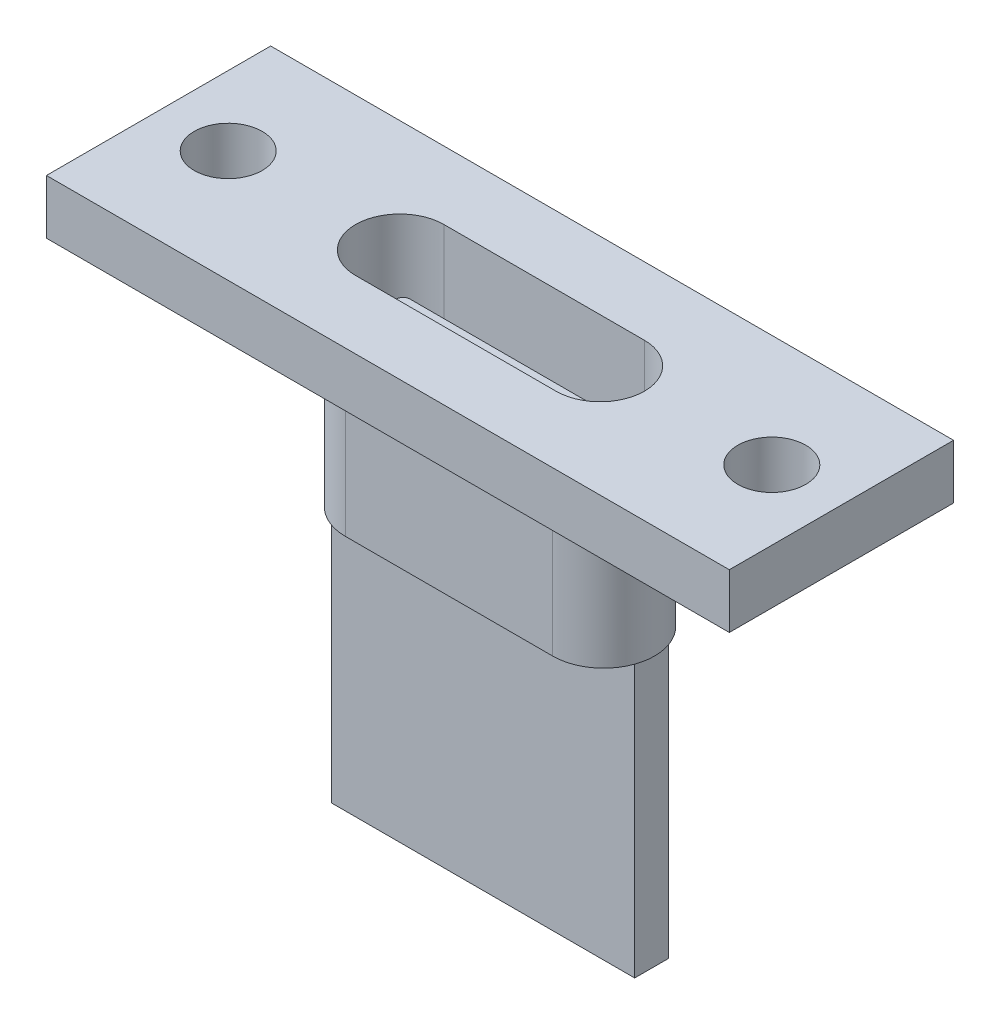
SolidWorks part; units mm, degrees
ref_plane "前视基准面" through (0, 0, 0) normal (0, 0, 1) x (1, 0, 0)
ref_plane "上视基准面" through (0, 0, 0) normal (0, 1, 0) x (1, 0, 0)
ref_plane "右视基准面" through (0, 0, 0) normal (1, 0, 0) x (0, 0, -1)
other "Configuration Table"
sketch "草图1" plane through (0, 0, 0) normal (0, 1, 0) x (1, 0, 0)
  line L1 (-10.05, -3.3) -> (10.05, -3.3)
  line L2 (-10.05, -3.3) -> (-10.05, 3.3)
  line L3 (-10.05, 3.3) -> (10.05, 3.3)
  line L4 (10.05, -3.3) -> (10.05, 3.3)
  line L5 (-10.05, -3.3) -> (10.05, 3.3) construction
  line L6 (-10.05, 3.3) -> (10.05, -3.3) construction
  point P0 (0, 0)
  dimension "D1" = 20.1
  dimension "D2" = 6.6
extrude "凸台-拉伸1" add sketch "草图1" along normal blind 1.6
sketch "草图2" plane through (0, 1.6, 0) normal (0, 1, 0) x (1, 0, 0)
  line L0 (-10.05, 0) -> (10.05, 0) construction
  line L1 (0, 3.3) -> (0, -3.3) construction
  line L2 (10.05, 3.3) -> (-10.05, 3.3) construction
  line L4 (10.05, -3.3) -> (10.05, 3.3)
  line L5 (10.05, 3.3) -> (-10.05, 3.3)
  line L6 (-10.05, 3.3) -> (-10.05, -3.3)
  line L7 (-10.05, -3.3) -> (10.05, -3.3)
  line L8 (10.05, -3.3) -> (10.05, 3.3) construction
  line L9 (10.05, 3.3) -> (-10.05, 3.3) construction
  line L10 (-10.05, 3.3) -> (-10.05, -3.3) construction
  line L11 (-10.05, -3.3) -> (10.05, -3.3) construction
  circle A0 centre (8, 0) radius 1
  circle A1 centre (-8, 0) radius 1
  dimension "D2" = 2
  dimension "D3" = 16
  dimension "D1" = 0
extrude "切除-拉伸1" cut sketch "草图2" against normal up to next
sketch "草图3" plane through (0, 0, 0) normal (0, -1, 0) x (1, 0, 0)
  line L0 (0, 3.3) -> (0, -3.3) construction
  line L1 (-10.05, 0) -> (10.05, 0) construction
  line L2 (-3.05, 0) -> (3.05, 0) construction
  line L3 (-3.05, 1.5) -> (3.05, 1.5)
  line L4 (10.05, -3.3) -> (10.05, 3.3)
  line L5 (10.05, 3.3) -> (-10.05, 3.3)
  line L6 (-10.05, 3.3) -> (-10.05, -3.3)
  line L7 (-10.05, -3.3) -> (10.05, -3.3)
  line L8 (10.05, -3.3) -> (10.05, 3.3) construction
  line L9 (10.05, 3.3) -> (-10.05, 3.3) construction
  line L10 (-10.05, 3.3) -> (-10.05, -3.3) construction
  line L11 (-10.05, -3.3) -> (10.05, -3.3) construction
  line L12 (-3.05, -1.5) -> (3.05, -1.5)
  arc A0 (-3.05, 1.5) -> (-3.05, -1.5) centre (-3.05, 0) ccw
  arc A1 (3.05, -1.5) -> (3.05, 1.5) centre (3.05, 0) ccw
  point P10 (0, 0)
  point P15 (0, 0)
  dimension "D2" = 6.1
  dimension "D3" = 1.5
  dimension "D1" = 0
extrude "凸台-拉伸2" add sketch "草图3" along normal blind 5
sketch "草图4" plane through (0, -5, 0) normal (0, -1, 0) x (1, 0, 0)
  line L1 (-4.4642, -0.5) -> (4.4642, -0.5)
  line L2 (-3.05, -1.5) -> (3.05, -1.5)
  line L3 (3.05, 1.5) -> (-3.05, 1.5)
  line L4 (-3.05, -1.5) -> (3.05, -1.5) construction
  line L5 (3.05, 1.5) -> (-3.05, 1.5) construction
  line L6 (-4.4642, -0.5) -> (-4.4642, 0.5)
  line L7 (-4.4642, 0.5) -> (4.4642, 0.5)
  line L8 (4.4642, -0.5) -> (4.4642, 0.5)
  line L9 (-4.4642, -0.5) -> (4.4642, 0.5) construction
  line L10 (-4.4642, 0.5) -> (4.4642, -0.5) construction
  arc A2 (-3.05, 1.5) -> (-3.05, -1.5) centre (-3.05, 0) ccw
  arc A3 (3.05, -1.5) -> (3.05, 1.5) centre (3.05, 0) ccw
  arc A4 (-3.05, 1.5) -> (-3.05, -1.5) centre (-3.05, 0) ccw construction
  arc A5 (3.05, -1.5) -> (3.05, 1.5) centre (3.05, 0) ccw construction
  point P0 (0, 0)
  dimension "D2" = 1
  dimension "D1" = 0
extrude "凸台-拉伸3" add sketch "草图4" along normal blind 8
sketch "草图5" plane through (0, 1.6, 0) normal (0, 1, 0) x (1, 0, 0)
  line L0 (-10.05, 0) -> (10.05, 0) construction
  line L1 (0, 3.3) -> (0, -3.3) construction
  line L2 (-2.95, 0) -> (2.95, 0) construction
  line L3 (-2.95, 1.3) -> (2.95, 1.3)
  line L4 (10.05, -3.3) -> (10.05, 3.3)
  line L5 (10.05, 3.3) -> (-10.05, 3.3)
  line L6 (-10.05, 3.3) -> (-10.05, -3.3)
  line L7 (-10.05, -3.3) -> (10.05, -3.3)
  line L8 (10.05, -3.3) -> (10.05, 3.3) construction
  line L9 (10.05, 3.3) -> (-10.05, 3.3) construction
  line L10 (-10.05, 3.3) -> (-10.05, -3.3) construction
  line L11 (-10.05, -3.3) -> (10.05, -3.3) construction
  line L12 (-2.95, -1.3) -> (2.95, -1.3)
  arc A1 (-2.95, 1.3) -> (-2.95, -1.3) centre (-2.95, 0) ccw
  arc A2 (2.95, -1.3) -> (2.95, 1.3) centre (2.95, 0) ccw
  point P10 (0, 0)
  point P15 (0, 0)
  point P16 (0, 0)
  dimension "D2" = 1.3
  dimension "D3" = 5.9
  dimension "D1" = 0
extrude "切除-拉伸2" cut sketch "草图5" against normal blind 5
sketch "草图6" plane through (0, -3.4, 0) normal (0, 1, 0) x (1, 0, 0)
  line L1 (-3.05, -0.4) -> (3.05, -0.4)
  line L2 (-2.95, -1.3) -> (2.95, -1.3)
  line L3 (2.95, 1.3) -> (-2.95, 1.3)
  line L4 (-2.95, -1.3) -> (2.95, -1.3) construction
  line L5 (2.95, 1.3) -> (-2.95, 1.3) construction
  line L6 (-3.25, -0.2) -> (-3.25, 0.2)
  line L7 (-3.05, 0.4) -> (3.05, 0.4)
  line L8 (3.25, -0.2) -> (3.25, 0.2)
  line L9 (-3.25, -0.4) -> (3.25, 0.4) construction
  line L10 (-3.25, 0.4) -> (3.25, -0.4) construction
  arc A0 (3.05, 0.4) -> (3.25, 0.2) centre (3.05, 0.2) cw
  arc A1 (3.05, -0.4) -> (3.25, -0.2) centre (3.05, -0.2) ccw
  arc A2 (-2.95, 1.3) -> (-2.95, -1.3) centre (-2.95, 0) ccw
  arc A3 (2.95, -1.3) -> (2.95, 1.3) centre (2.95, 0) ccw
  arc A4 (-2.95, 1.3) -> (-2.95, -1.3) centre (-2.95, 0) ccw construction
  arc A5 (2.95, -1.3) -> (2.95, 1.3) centre (2.95, 0) ccw construction
  arc A6 (-3.05, -0.4) -> (-3.25, -0.2) centre (-3.05, -0.2) cw
  arc A7 (-3.25, 0.2) -> (-3.05, 0.4) centre (-3.05, 0.2) cw
  point P0 (0, 0)
  dimension "D4" = 0.2
  dimension "D2" = 0.8
  dimension "D3" = 6.5
  dimension "D1" = 0
extrude "凸台-拉伸4" add sketch "草图6" along normal blind 3.5
